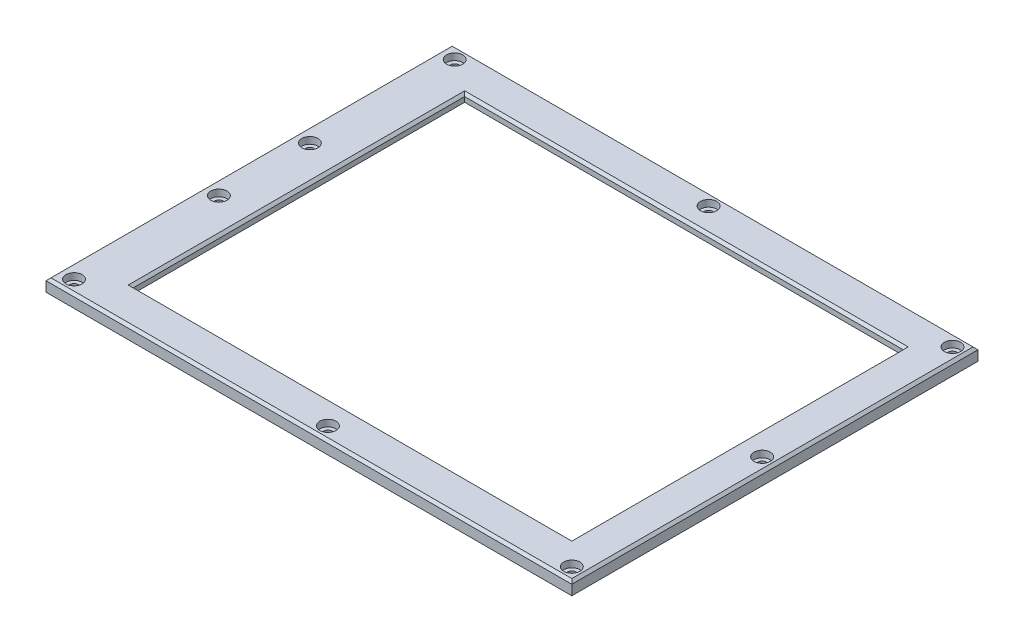
SolidWorks part; units mm, degrees
ref_plane "Front Plane" through (0, 0, 0) normal (0, 0, 1) x (1, 0, 0)
ref_plane "Top Plane" through (0, 0, 0) normal (0, 1, 0) x (1, 0, 0)
ref_plane "Right Plane" through (0, 0, 0) normal (1, 0, 0) x (0, 0, -1)
sketch "Sketch1" plane through (0, 0, 0) normal (0, 1, 0) x (1, 0, 0)
  line L1 (-88, -66.5) -> (88, -66.5)
  line L2 (-88, -66.5) -> (-88, 66.5)
  line L3 (-88, 66.5) -> (88, 66.5)
  line L4 (88, -66.5) -> (88, 66.5)
  line L5 (-88, -66.5) -> (88, 66.5) construction
  line L6 (-88, 66.5) -> (88, -66.5) construction
  line L7 (-108, -81.5) -> (103, -81.5)
  line L8 (-108, -81.5) -> (-108, 81.5)
  line L9 (-108, 81.5) -> (103, 81.5)
  line L10 (103, -81.5) -> (103, 81.5)
  point P0 (0, 0)
  point P6 (0, 0)
  dimension "D1" = 133
  dimension "D2" = 176
  dimension "D3" = 15
  dimension "D4" = 20
  dimension "D5" = 15
  dimension "D6" = 15
extrude "Boss-Extrude1" add sketch "Sketch1" along normal blind 5 contours L8 L7 L10 L9 | L2 L1 L4 L3
sketch "Sketch2" plane through (0, 5, 0) normal (0, 1, 0) x (1, 0, 0)
  line L0 (-108, -81.5) -> (-108, 81.5) construction
  line L1 (-95.75, -71.25) -> (92.75, -71.25)
  line L2 (-95.75, -71.25) -> (-95.75, -10.25)
  line L3 (-95.75, 71.25) -> (92.75, 71.25)
  line L4 (92.75, -71.25) -> (92.75, 71.25)
  line L7 (-95.75, 10.25) -> (-102.25, 10.25)
  line L9 (-95.75, -10.25) -> (-102.25, -10.25)
  line L10 (-102.25, 10.25) -> (-102.25, 6.75)
  line L11 (-102.25, 6.75) -> (-108, 6.75)
  line L13 (-102.25, -6.75) -> (-108, -6.75)
  line L14 (-108, 6.75) -> (-108, -6.75)
  line L15 (-102.25, -6.75) -> (-102.25, -10.25)
  line L16 (-95.75, 10.25) -> (-95.75, 71.25)
  line L17 (-102.25, 10.25) -> (-102.25, -10.25) construction
  line L23 (88, -66.5) -> (88, 66.5) construction
  line L24 (-88, -66.5) -> (88, -66.5) construction
  point P0 (0, 0)
  point P10 (-108, 0)
  point P17 (-102.25, 0)
  point P18 (92.75, 0)
  dimension "D1" = 188.5
  dimension "D2" = 142.5
  dimension "D3" = 20.5
  dimension "D4" = 6.5
  dimension "D5" = 13.5
  dimension "D6" = 4.75
  dimension "D7" = 4.75
extrude "Cut-Extrude1" cut sketch "Sketch2" along normal blind 2 from surface at -5 starting at face at (0, 0, 0)
hole_wizard "CBORE for M3 SHCS1" positions "Sketch5" profile "Sketch6" counterbore size "M3" standard "ANSI Metric" end condition up to next
sketch "Sketch5" plane through (0, 5, 0) normal (0, 1, 0) x (1, 0, 0)
  line L0 (-108, -81.5) -> (103, -81.5) construction
  line L1 (-95.75, -71.25) -> (92.75, -71.25) construction
  line L2 (0, -81.5) -> (0, -71.25) construction
  line L4 (0, 81.5) -> (0, 71.25) construction
  line L5 (-108, 81.5) -> (103, 81.5) construction
  line L6 (92.75, 71.25) -> (-95.75, 71.25) construction
  line L8 (-95.75, -71.25) -> (-95.75, -81.5) construction
  line L10 (-95.75, -71.25) -> (-108, -71.25) construction
  line L11 (-108, -81.5) -> (-108, -6.75) construction
  line L13 (92.75, -71.25) -> (92.75, -81.5) construction
  line L15 (92.75, -71.25) -> (103, -71.25) construction
  line L16 (103, -81.5) -> (103, 81.5) construction
  line L18 (-102.25, -10.25) -> (-95.75, -10.25) construction
  line L19 (-95.75, 10.25) -> (-102.25, 10.25) construction
  point P0 (-101.875, 76.375)
  point P2 (0, 76.375)
  point P4 (97.875, 76.375)
  point P6 (97.875, -76.375)
  point P8 (97.875, 0)
  point P10 (0, -76.375)
  point P12 (-101.875, -76.375)
  point P14 (-101.875, -18.25)
  point P16 (-101.875, 18.25)
  point P65 (-101.875, -71.25)
  point P79 (97.875, -71.25)
  dimension "D1" = 8
  dimension "D2" = 8
sketch "Sketch6" plane through (-101.875, 5, -76.375) normal (1, 0, 0) x (0, 0, 1)
  line L0 (0, 0) -> (0, 5)
  line L1 (0, 5) -> (1.7, 5)
  line L3 (1.7, 5) -> (1.7, 2.68)
  line L4 (1.7, 2.68) -> (3.25, 2.68)
  line L5 (3.25, 2.68) -> (3.25, 0)
  line L7 (3.25, 0) -> (0, 0)
  line L11 (0, -6.35) -> (0, 107.95) construction
  dimension "Thru Hole Dia." = 3.4
  dimension "Thru Hole Depth" = 5
  dimension "C'Bore Dia." = 6.5
  dimension "C'Bore Depth" = 2.68
chamfer "Chamfer2" distance 1 angle 45 8 edges at (-88, 5, 0) (0, 5, 66.5) (88, 5, 0) (0, 5, -66.5) (-108, 5, 0) (-2.5, 5, -81.5) (103, 5, 0) (-2.5, 5, 81.5)
